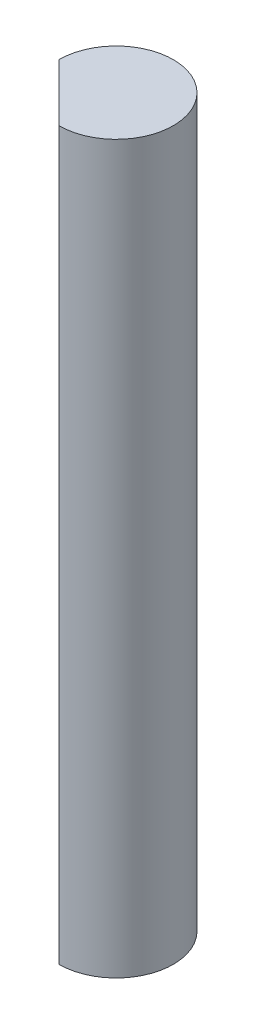
SolidWorks part; units mm, degrees
ref_plane "Front Plane" through (0, 0, 0) normal (0, 0, 1) x (1, 0, 0)
ref_plane "Top Plane" through (0, 0, 0) normal (0, 1, 0) x (1, 0, 0)
ref_plane "Right Plane" through (0, 0, 0) normal (1, 0, 0) x (0, 0, -1)
sketch "Sketch1" plane through (0, 0, 0) normal (0, 1, 0) x (1, 0, 0)
  line L0 (-4, 0) -> (0, -4)
  arc A0 (0, -4) -> (-4, 0) centre (0, 0) ccw
extrude "Boss-Extrude1" add sketch "Sketch1" along normal blind 50.8
